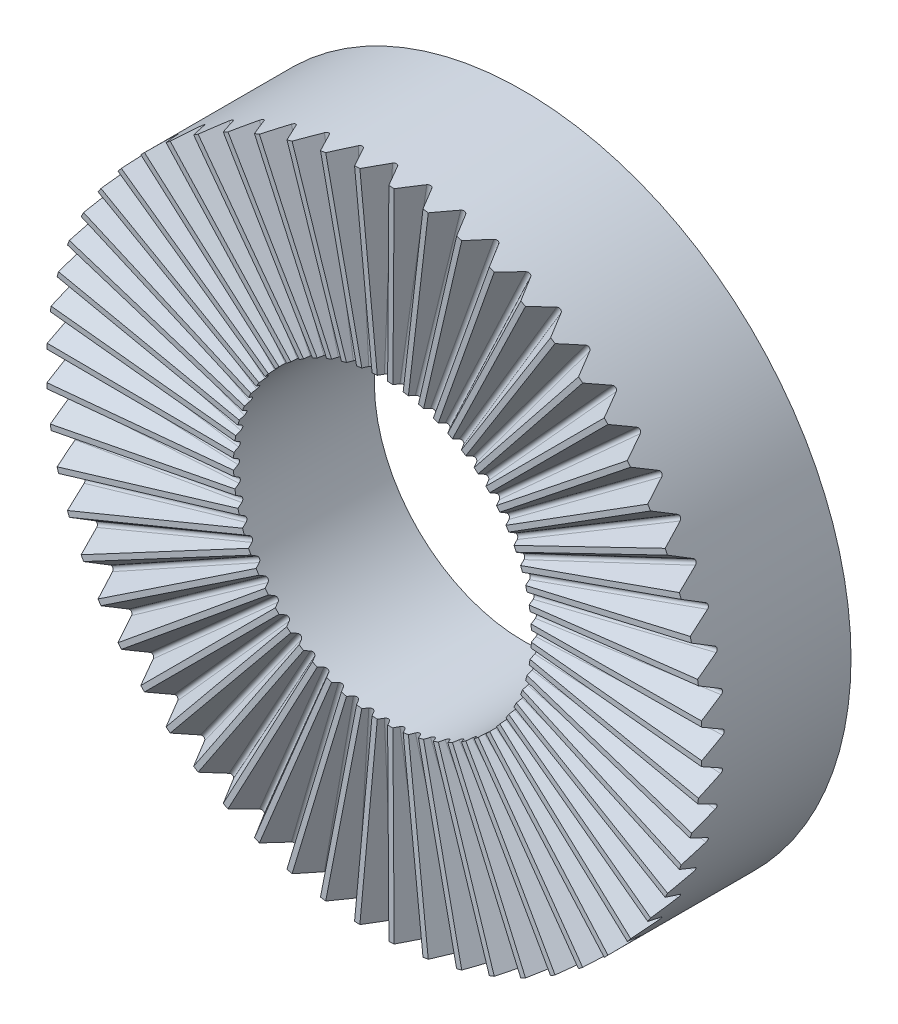
SolidWorks part; units mm, degrees
ref_plane "Ebene vorne" through (0, 0, 0) normal (0, 0, 1) x (1, 0, 0)
ref_plane "Ebene oben" through (0, 0, 0) normal (0, 1, 0) x (1, 0, 0)
ref_plane "Ebene rechts" through (0, 0, 0) normal (1, 0, 0) x (0, 0, -1)
sketch "Skizze1" plane through (0, 0, 0) normal (0, 0, 1) x (1, 0, 0)
  circle A0 centre (0, 0) radius 5
  circle A1 centre (0, 0) radius 11
  dimension "D1" = 10
  dimension "D2" = 22
extrude "Aufsatz-Linear austragen1" add sketch "Skizze1" along normal blind 5
sketch "Skizze2" plane through (0, 0, 0) normal (1, 0, 0) x (0, 0, -1)
  line L0 (-2.5, 11) -> (-2.5, -11) construction
  line L1 (0, 11) -> (-5, 11) construction
  line L2 (-5, -11) -> (0, -11) construction
ref_plane "Ebene1" through (0.1133, 0, 0.0051) normal (0.999, 0, 0.0454) x (0, -1, 0)
sketch "Skizze3" plane through (0.1133, 0, 0.0051) normal (0.999, 0, 0.0454) x (0, -1, 0)
  line L0 (0, -4.85) -> (0, 0) construction
  line L1 (1.1258, -6.6) -> (0.0866, -4.8)
  line L2 (-0.0866, -4.8) -> (-1.1258, -6.6)
  line L3 (-1.1258, -6.6) -> (1.1258, -6.6)
  line L4 (-0.0866, -4.8) -> (0.0866, -4.8) construction
  arc A0 (0.0866, -4.8) -> (-0.0866, -4.8) centre (0, -4.85) ccw
  dimension "D2" = 0.1
  dimension "D1" = 60
  dimension "D3" = 4.85
  dimension "D4" = 1.75
extrude "Schnitt-Linear austragen1" cut sketch "Skizze3" against normal through all
pattern_circular "Kreismuster2" count 60 over 360 about axis through (0, 0, 0) along (0, 0, 1) of "Schnitt-Linear austragen1"
sketch "Skizze4" plane through (0, 0, 0) normal (1, 0, 0) x (0, 0, -1)
  line L0 (-5, 11) -> (-4.5005, 0)
  line L1 (-4.5005, 0) -> (-5, 0)
  line L2 (-5, 0) -> (-5, 11)
  line L3 (0, -11) -> (0, 11) construction
  line L4 (0, 0) -> (-12.4663, 0) construction
  dimension "D1" = 2.6
  dimension "D2" = 5
  dimension "D3" = 11
revolve "Schnitt-Rotation1" cut sketch "Skizze4" angle 360 about axis through (0, 0, 5) along (0, 0, -1)
